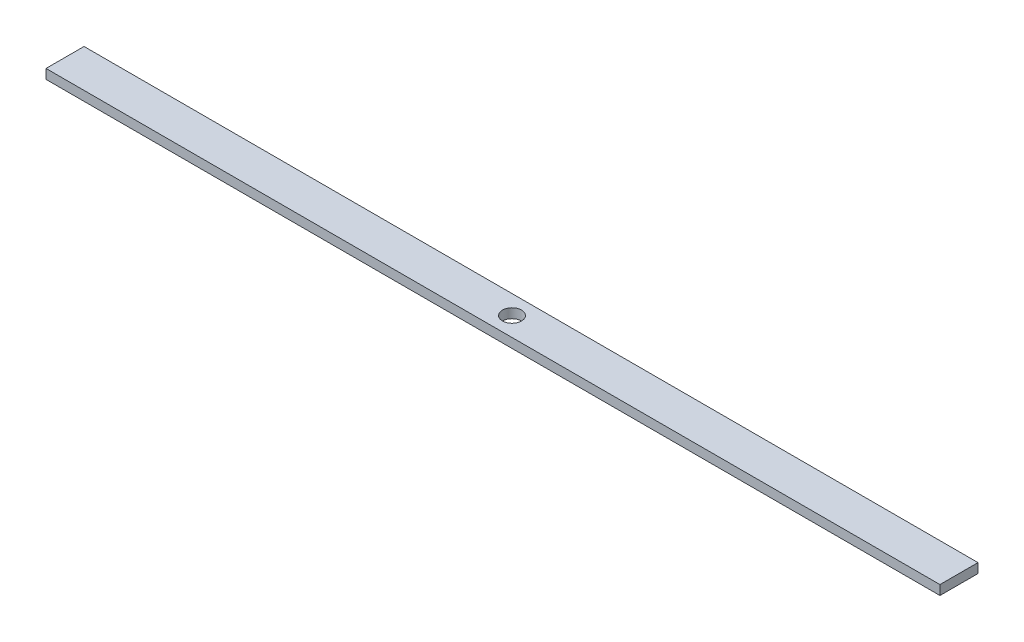
SolidWorks part; units mm, degrees
material "6061-T6 (SS)"
ref_plane "Front Plane" through (0, 0, 0) normal (0, 0, 1) x (1, 0, 0)
ref_plane "Top Plane" through (0, 0, 0) normal (0, 1, 0) x (1, 0, 0)
ref_plane "Right Plane" through (0, 0, 0) normal (1, 0, 0) x (0, 0, -1)
sketch "Sketch1" plane through (0, 0, 0) normal (0, 1, 0) x (1, 0, 0)
  line L1 (-298.45, 12.7) -> (298.45, 12.7)
  line L2 (-298.45, 12.7) -> (-298.45, -12.7)
  line L3 (-298.45, -12.7) -> (298.45, -12.7)
  line L4 (298.45, 12.7) -> (298.45, -12.7)
  line L5 (-298.45, 12.7) -> (298.45, -12.7) construction
  line L6 (-298.45, -12.7) -> (298.45, 12.7) construction
  circle A0 centre (0, 0) radius 6.35
  point P0 (0, 0)
  dimension "D1" = 596.9
  dimension "D2" = 25.4
extrude "Boss-Extrude1" add sketch "Sketch1" along normal blind 6.35
